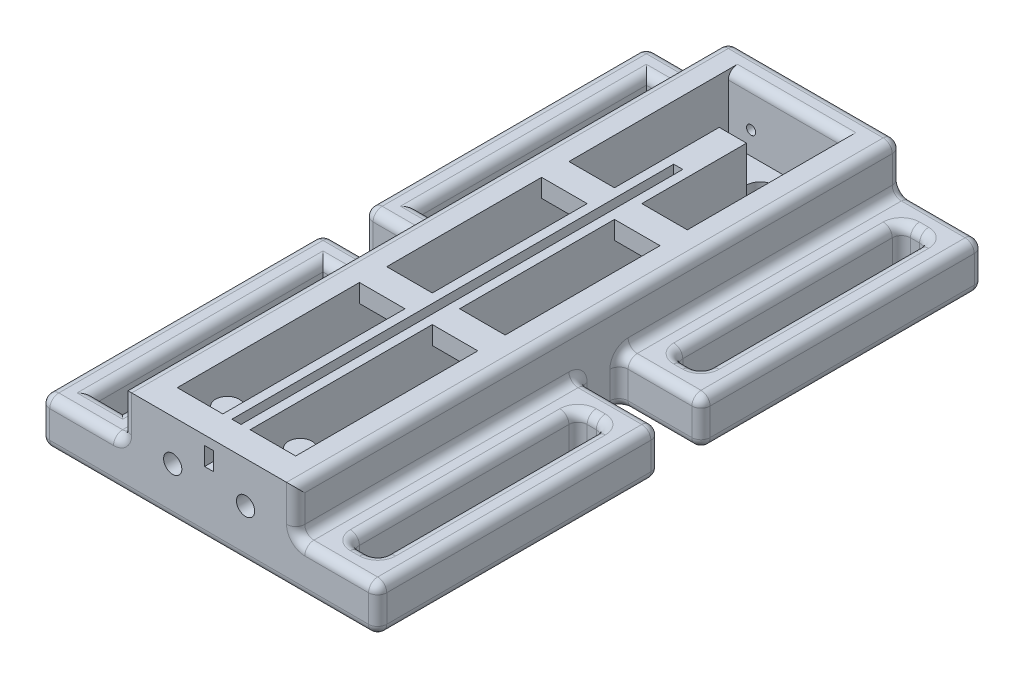
SolidWorks part; units mm, degrees
ref_plane "Front Plane" through (0, 0, 0) normal (0, 0, 1) x (1, 0, 0)
ref_plane "Top Plane" through (0, 0, 0) normal (0, 1, 0) x (1, 0, 0)
ref_plane "Right Plane" through (0, 0, 0) normal (1, 0, 0) x (0, 0, -1)
sketch "Sketch1" plane through (0, 0, 0) normal (0, 1, 0) x (1, 0, 0)
  line L1 (0, 0) -> (19, 0)
  line L2 (0, 0) -> (0, 66.5)
  line L3 (0, 66.5) -> (19, 66.5)
  line L4 (19, 0) -> (19, 66.5)
extrude "Boss-Extrude2" add sketch "Sketch1" along normal blind 10 contours L3 L4 L1 L2
sketch "Sketch2" plane through (0, 10, 0) normal (0, 1, 0) x (1, 0, 0)
  line L0 (8, 63.5) -> (8, 3)
  line L1 (3, 3) -> (16, 3)
  line L2 (3, 3) -> (3, 63.5)
  line L3 (3, 63.5) -> (16, 63.5)
  line L4 (0, 66.5) -> (19, 66.5) construction
  line L5 (11, 63.5) -> (11, 3)
  line L6 (16, 63.5) -> (16, 3)
  line L12 (0, 0) -> (0, 66.5) construction
  line L14 (0, 0) -> (19, 0) construction
  dimension "D1" = 3
  dimension "D2" = 3
  dimension "D5" = 5
  dimension "D6" = 5
  dimension "D10" = 3
  dimension "D11" = 3
extrude "Cut-Extrude1" cut sketch "Sketch2" against normal blind 7 contours L3 L2 L1 L0 | L6 L3 L5 L1
sketch "Sketch3" plane through (0, 0, 0) normal (0, 1, 0) x (1, 0, 0)
  line L0 (0, 0) -> (0, 66.5) construction
  line L1 (0, 0) -> (-9, 0)
  line L2 (0, 0) -> (0, 31)
  line L3 (0, 31) -> (-9, 31)
  line L4 (-9, 0) -> (-9, 31)
  line L5 (19, 0) -> (28, 0)
  line L6 (19, 0) -> (19, 31)
  line L7 (19, 31) -> (28, 31)
  line L8 (28, 0) -> (28, 31)
  line L17 (0, 66.5) -> (-9, 66.5)
  line L18 (0, 66.5) -> (0, 35.5)
  line L19 (0, 35.5) -> (-9, 35.5)
  line L20 (-9, 66.5) -> (-9, 35.5)
  line L21 (19, 0) -> (19, 66.5) construction
  line L22 (19, 66.5) -> (28, 66.5)
  line L23 (19, 66.5) -> (19, 35.5)
  line L24 (19, 35.5) -> (28, 35.5)
  line L25 (28, 66.5) -> (28, 35.5)
  line L27 (-6, 28) -> (-3, 28)
  line L28 (-6, 28) -> (-6, 3)
  line L29 (-6, 3) -> (-3, 3)
  line L30 (-3, 28) -> (-3, 3)
  line L31 (22, 28) -> (25, 28)
  line L32 (22, 28) -> (22, 3)
  line L33 (22, 3) -> (25, 3)
  line L34 (25, 28) -> (25, 3)
  line L39 (22, 63.5) -> (25, 63.5)
  line L40 (22, 63.5) -> (22, 38.5)
  line L41 (22, 38.5) -> (25, 38.5)
  line L42 (25, 63.5) -> (25, 38.5)
  line L43 (-6, 63.5) -> (-3, 63.5)
  line L44 (-6, 63.5) -> (-6, 38.5)
  line L45 (-6, 38.5) -> (-3, 38.5)
  line L46 (-3, 63.5) -> (-3, 38.5)
  dimension "D13" = 3
  dimension "D14" = 3
  dimension "D15" = 25
  dimension "D16" = 3
  dimension "D17" = 3
  dimension "D18" = 3
  dimension "D19" = 3
  dimension "D20" = 3
  dimension "D21" = 3
  dimension "D22" = 3
  dimension "D23" = 25
  dimension "D24" = 3
  dimension "D25" = 25
  dimension "D26" = 3
  dimension "D27" = 3
  dimension "D28" = 3
  dimension "D29" = 3
  dimension "D30" = 3
  dimension "D31" = 3
  dimension "D32" = 3
  dimension "D33" = 3
  dimension "D34" = 3
  dimension "D35" = 3
  dimension "D36" = 25
  dimension "D40" = 4.5
extrude "Boss-Extrude3" add sketch "Sketch3" along normal blind 5
sketch "Sketch4" plane through (0, 3, 0) normal (0, 1, 0) x (1, 0, 0)
  line L0 (11, 63.5) -> (11, 3) construction
  line L1 (8, 63.5) -> (8, 3) construction
  line L2 (11, 3) -> (16, 3) construction
  line L3 (3, 3) -> (8, 3) construction
  circle A0 centre (5.5, 6) radius 1.3
  circle A1 centre (13.5, 6) radius 1.3
  dimension "D1" = 2.5
  dimension "D2" = 2.5
  dimension "D3" = 3
  dimension "D4" = 3
extrude "Boss-Extrude4" add sketch "Sketch4" along normal blind 5
sketch "Sketch5" plane through (0, 10, 0) normal (0, 1, 0) x (1, 0, 0)
  line L0 (3, 3) -> (3, 63.5) construction
  line L1 (3, 23) -> (16, 23)
  line L2 (3, 23) -> (3, 26)
  line L3 (3, 26) -> (16, 26)
  line L4 (16, 23) -> (16, 26)
  line L5 (16, 63.5) -> (16, 3) construction
  line L7 (3, 43) -> (16, 43)
  line L8 (3, 43) -> (3, 46)
  line L9 (3, 46) -> (16, 46)
  line L10 (16, 43) -> (16, 46)
  circle A0 centre (5.5, 6) radius 1.3 construction
  dimension "D1" = 17
  dimension "D2" = 3
  dimension "D3" = 37
  dimension "D4" = 3
extrude "Boss-Extrude5" add sketch "Sketch5" against normal blind 2
sketch "Sketch6" plane through (0, 10, 0) normal (0, 1, 0) x (1, 0, 0)
  line L0 (8, 46) -> (3, 46) construction
  line L4 (11, 63.5) -> (11, 3) construction
  circle A0 centre (9.5, 60.5) radius 1.51
  dimension "D1" = 14.5
  dimension "D7" = 1.5
extrude "Cut-Extrude4" cut sketch "Sketch6" against normal blind 10
sketch "Sketch7" plane through (0, 10, 0) normal (0, 1, 0) x (1, 0, 0)
  line L0 (8, 63.5) -> (8, 60.6735) construction
  line L1 (8, 63.5) -> (11, 63.5)
  line L2 (8, 63.5) -> (8, 57.5)
  line L3 (8, 57.5) -> (11, 57.5)
  line L4 (11, 63.5) -> (11, 57.5)
  line L5 (11, 60.3265) -> (11, 46) construction
  arc A0 (11, 60.6735) -> (8, 60.6735) centre (9.5, 60.5) ccw construction
  arc A1 (8, 60.3265) -> (11, 60.3265) centre (9.5, 60.5) ccw construction
  dimension "D1" = 3
  dimension "D2" = 3
extrude "Cut-Extrude5" cut sketch "Sketch7" against normal blind 7
sketch "Sketch10" plane through (0, 0, -66.5) normal (0, 0, 1) x (1, 0, 0)
  line L1 (16, 3) -> (16, 10) construction
  line L2 (3, 3) -> (3, 10) construction
  line L6 (3, 3) -> (16, 3) construction
  circle A0 centre (5.5, 5.5) radius 0.5
  circle A1 centre (13.5, 5.5) radius 0.5
  dimension "D1" = 2.5
  dimension "D2" = 2.5
  dimension "D3" = 2.5
  dimension "D4" = 2.5
extrude "Cut-Extrude6" cut sketch "Sketch10" along normal blind 3
sketch "Sketch11" plane through (0, 0, -3) normal (0, 0, -1) x (-1, 0, 0)
  line L4 (-16, 3) -> (-16, 10) construction
  line L5 (-11, 3) -> (-16, 3) construction
  line L6 (-3, 3) -> (-8, 3) construction
  line L7 (-8, 3) -> (-8, 10) construction
  circle A2 centre (-13.5, 5.5) radius 1
  circle A3 centre (-5.5, 5.5) radius 1
  dimension "D5" = 2.5
  dimension "D6" = 2.5
  dimension "D7" = 2.5
  dimension "D8" = 2.5
extrude "Cut-Extrude7" cut sketch "Sketch11" against normal blind 3
sketch "Sketch12" plane through (0, 10, 0) normal (0, 1, 0) x (1, 0, 0)
  line L5 (0, 0) -> (19, 0) construction
  line L6 (8, 57.5) -> (11, 57.5) construction
  line L7 (9, 0) -> (10, 0)
  line L8 (9, 0) -> (9, 57.5)
  line L9 (9, 57.5) -> (10, 57.5)
  line L10 (10, 0) -> (10, 57.5)
  line L13 (11, 57.5) -> (11, 46) construction
  line L14 (8, 57.5) -> (8, 46) construction
  line L44 (9, 0) -> (10, 0)
  line L45 (9, 0) -> (9, 3)
  line L46 (9, 3) -> (10, 3)
  line L47 (10, 0) -> (10, 3)
  line L49 (10, 14.5) -> (10, 11.5)
  line L51 (9, 14.5) -> (9, 11.5)
  line L53 (10, 26) -> (10, 23)
  line L55 (9, 26) -> (9, 23)
  line L57 (10, 36.4083) -> (10, 33.4371)
  line L59 (9, 36.4083) -> (9, 33.4371)
  line L61 (10, 46) -> (10, 43)
  line L63 (9, 46) -> (9, 43)
  line L65 (10, 55.5) -> (10, 52.5)
  line L67 (9, 55.5) -> (9, 52.5)
  line L68 (10, 54.5) -> (9, 54.5)
  line L69 (10, 54.5) -> (10, 51.5)
  line L70 (10, 51.5) -> (9, 51.5)
  line L71 (9, 54.5) -> (9, 51.5)
  line L79 (11, 3) -> (16, 3) construction
  dimension "D3" = 1
  dimension "D4" = 1
  dimension "D12" = 0
  dimension "D24" = 3
  dimension "D25" = 3
extrude "Cut-Extrude8" cut sketch "Sketch12" against normal blind 3
sketch "Sketch13" plane through (0, 0, -57.5) normal (0, 0, -1) x (-1, 0, 0)
  line L6 (-10, 9) -> (-9, 9)
  line L7 (-10, 9) -> (-10, 7)
  line L8 (-10, 7) -> (-9, 7)
  line L9 (-9, 9) -> (-9, 7)
extrude "Cut-Extrude9" cut sketch "Sketch13" against normal blind 68
fillet "Fillet1" radius 1 80 edges at (23.5, 0, -3) (23.5, 5, -3) (23.5, 0, -28) (23.5, 5, -28) (23.5, 0, -38.5) (23.5, 5, -38.5) (23.5, 0, -63.5) (23.5, 5, -63.5) (19, 7.5, -66.5) (0, 7.5, -66.5) (19, 2.5, -35.5) (23.5, 0, -35.5) (23.5, 5, -35.5) (23.5, 5, -31) (25, 2.5, -28) (25, 2.5, -3) (25, 0, -15.5) (25, 5, -15.5) (28, 2.5, 0) (28, 2.5, -31) (28, 0, -15.5) (28, 5, -15.5) (22, 2.5, -3) (22, 2.5, -28) (22, 0, -15.5) (22, 5, -15.5) (25, 2.5, -63.5) (25, 2.5, -38.5) (25, 0, -51) (25, 5, -51) (22, 2.5, -38.5) (22, 2.5, -63.5) (22, 0, -51) (22, 5, -51) (23.5, 5, -66.5) (19, 5, -51) (28, 2.5, -35.5) (28, 5, -51) (28, 2.5, -66.5) (28, 0, -51) (-4.5, 5, -31) (0, 2.5, -35.5) (-4.5, 0, -35.5) (-4.5, 5, -35.5) (-3, 5, -15.5) (-4.5, 5, -28) (-6, 5, -15.5) (-4.5, 5, -3) (-9, 2.5, -31) (-9, 5, -15.5) (-9, 2.5, 0) (-9, 0, -15.5) (-4.5, 5, -38.5) (-3, 5, -51) (-4.5, 5, -63.5) (-6, 5, -51) (-4.5, 5, -66.5) (0, 5, -51) (-9, 2.5, -66.5) (-9, 5, -51) (-9, 2.5, -35.5) (-9, 0, -51) (9.5, 10, -63.5) (9.5, 10, -66.5) (0, 10, -33.25) (19, 10, -33.25) (9.5, 0, 0) (9.5, 0, -66.5)
